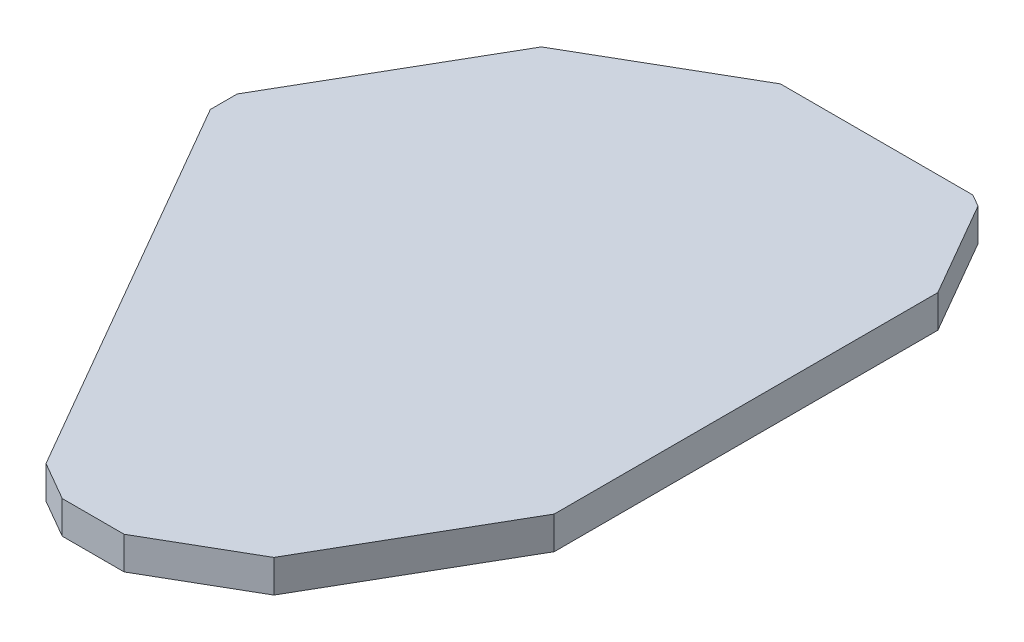
SolidWorks part; units mm, degrees
ref_plane "Ebene vorne" through (0, 0, 0) normal (0, 0, 1) x (1, 0, 0)
ref_plane "Ebene oben" through (0, 0, 0) normal (0, 1, 0) x (1, 0, 0)
ref_plane "Ebene rechts" through (0, 0, 0) normal (1, 0, 0) x (0, 0, -1)
sketch "Skizze1" plane through (0, 0, 0) normal (0, 1, 0) x (1, 0, 0)
  line L0 (0, 11) -> (0, 0) construction
  line L1 (0, 0) -> (6, 10.3923) construction
  line L2 (0, 0) -> (8.6603, 5) construction
  line L3 (0, 0) -> (7, 0) construction
  line L4 (0, 0) -> (6.9282, -4) construction
  line L5 (0, 0) -> (5.0003, -8.6607) construction
  line L6 (0, 0) -> (0, -11) construction
  line L7 (0, 0) -> (-5, -8.6603) construction
  line L8 (0, 0) -> (-6.0622, -3.5) construction
  line L9 (0, 0) -> (-9, 0) construction
  line L10 (0, 0) -> (-7.7942, 4.5) construction
  line L11 (0, 0) -> (-5, 8.6603) construction
  line L12 (-19.411, 11) -> (19.411, 11)
  line L13 (-10.2893, 19.7969) -> (22.2893, 0.9877)
  line L14 (-1.312, 22.2725) -> (18.6326, -12.2725)
  line L15 (7, 21.1846) -> (7, -21.1846)
  line L16 (17.342, 14.0372) -> (-3.4856, -22.0372)
  line L17 (-12.272, -18.6329) -> (22.2726, 1.3114)
  line L18 (-19.411, -11) -> (19.411, -11)
  line L19 (-22.2725, 1.312) -> (12.2725, -18.6326)
  line L20 (-16.6545, 14.8464) -> (4.5301, -21.8464)
  line L21 (-9, 20.4154) -> (-9, -20.4154)
  line L22 (-18.0019, -13.1802) -> (2.4135, 22.1802)
  line L23 (-22.2725, -1.312) -> (12.2725, 18.6326)
  arc A0 (7.1196, 4.1105) -> (4.1105, 7.1196) centre (0, 0) ccw construction
  arc A1 (4.1105, 7.1196) -> (0, 8.221) centre (0, 0) ccw construction
  arc A2 (0, 8.221) -> (-4.1105, 7.1196) centre (0, 0) ccw construction
  arc A3 (-4.1105, 7.1196) -> (-7.1196, 4.1105) centre (0, 0) ccw construction
  arc A4 (-7.1196, 4.1105) -> (-8.221, 0) centre (0, 0) ccw construction
  arc A5 (-8.221, 0) -> (-7.1196, -4.1105) centre (0, 0) ccw construction
  arc A6 (-7.1196, -4.1105) -> (-4.1105, -7.1196) centre (0, 0) ccw construction
  arc A7 (-4.1105, -7.1196) -> (0, -8.221) centre (0, 0) ccw construction
  arc A8 (0, -8.221) -> (4.1105, -7.1196) centre (0, 0) ccw construction
  arc A9 (4.1105, -7.1196) -> (7.1196, -4.1105) centre (0, 0) ccw construction
  arc A10 (7.1196, -4.1105) -> (8.221, 0) centre (0, 0) ccw construction
  arc A11 (8.221, 0) -> (7.1196, 4.1105) centre (0, 0) ccw construction
  circle A12 centre (0, 0) radius 22.3111
  dimension "D1" = 10
  dimension "D7" = 10.0006
  dimension "D2" = 11
  dimension "D3" = 12
  dimension "D4" = 10
  dimension "D5" = 7
  dimension "D6" = 8
  dimension "D8" = 11
  dimension "D9" = 10
  dimension "D10" = 7
  dimension "D11" = 9
  dimension "D12" = 9
extrude "Aufsatz-Linear austragen1" add sketch "Skizze1" along normal blind 1 contours L23 L22 L21 L20 L19 L18 L17 L16 L15 L14 L13 L12
